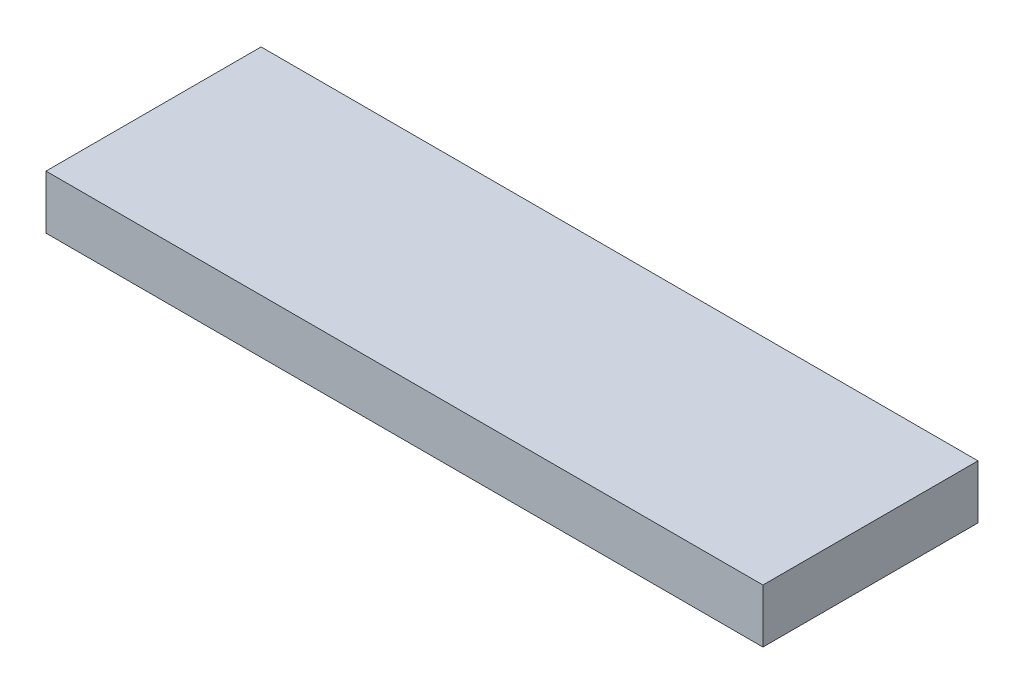
SolidWorks part; units mm, degrees
ref_plane "Front Plane" through (0, 0, 0) normal (0, 0, 1) x (1, 0, 0)
ref_plane "Top Plane" through (0, 0, 0) normal (0, 1, 0) x (1, 0, 0)
ref_plane "Right Plane" through (0, 0, 0) normal (1, 0, 0) x (0, 0, -1)
sketch "Sketch2" plane through (0, 0, 0) normal (0, 1, 0) x (1, 0, 0)
  line L1 (-100, -30) -> (100, -30)
  line L2 (-100, -30) -> (-100, 30)
  line L3 (-100, 30) -> (100, 30)
  line L4 (100, -30) -> (100, 30)
  line L5 (-100, -30) -> (100, 30) construction
  line L6 (-100, 30) -> (100, -30) construction
  point P0 (0, 0)
  dimension "D1" = 200
  dimension "D2" = 60
extrude "Boss-Extrude2" add sketch "Sketch2" along normal blind 15
sketch "Sketch3" plane through (0, 15, 0) normal (0, 1, 0) x (1, 0, 0)
  line L0 (-100, 0) -> (100, 0) construction
  line L1 (-100, 30) -> (-100, -30) construction
  line L2 (100, -30) -> (100, 30) construction
  line L3 (0, 30) -> (0, -30) construction
  line L4 (100, 30) -> (-100, 30) construction
  line L5 (-100, -30) -> (100, -30) construction
  line L6 (-75, 30) -> (-75, -30) construction
  line L7 (75, 30) -> (75, -30) construction
  line L8 (-75, 30) -> (75, 30) construction
  point P16 (0, 30)
  dimension "D1" = 150
